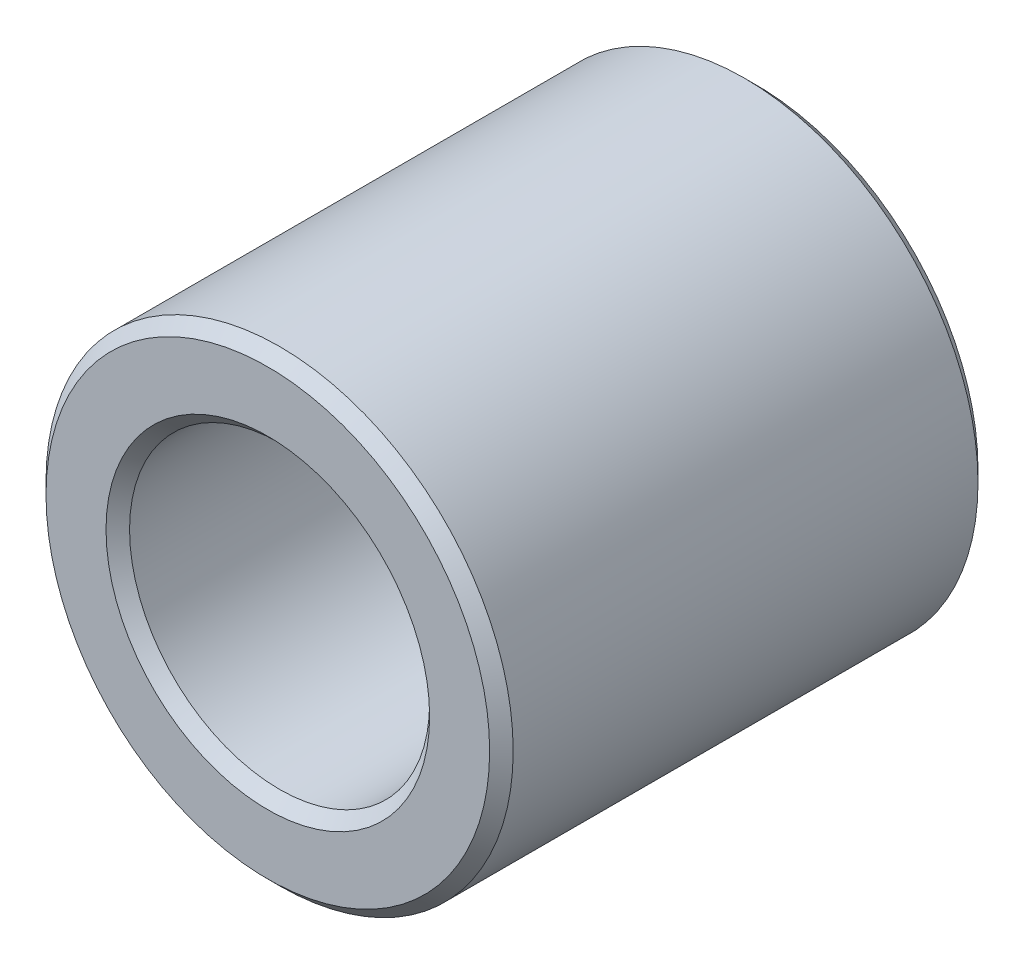
SolidWorks part; units mm, degrees
material "6061-T6 (SS)"
ref_plane "Front Plane" through (0, 0, 0) normal (0, 0, 1) x (1, 0, 0)
ref_plane "Top Plane" through (0, 0, 0) normal (0, 1, 0) x (1, 0, 0)
ref_plane "Right Plane" through (0, 0, 0) normal (1, 0, 0) x (0, 0, -1)
sketch "Sketch1" plane through (0, 0, 0) normal (0, 0, 1) x (1, 0, 0)
  circle A0 centre (0, 0) radius 2.55
  circle A1 centre (0, 0) radius 3.97
  dimension "D1" = 5.1
  dimension "D2" = 7.94
extrude "Boss-Extrude1" add sketch "Sketch1" along normal blind 8.3
chamfer "Chamfer1" distance 0.2 angle 45 4 edges at (3.97, 0, 0) (2.55, 0, 0) (2.55, 0, 8.3) (3.97, 0, 8.3)
